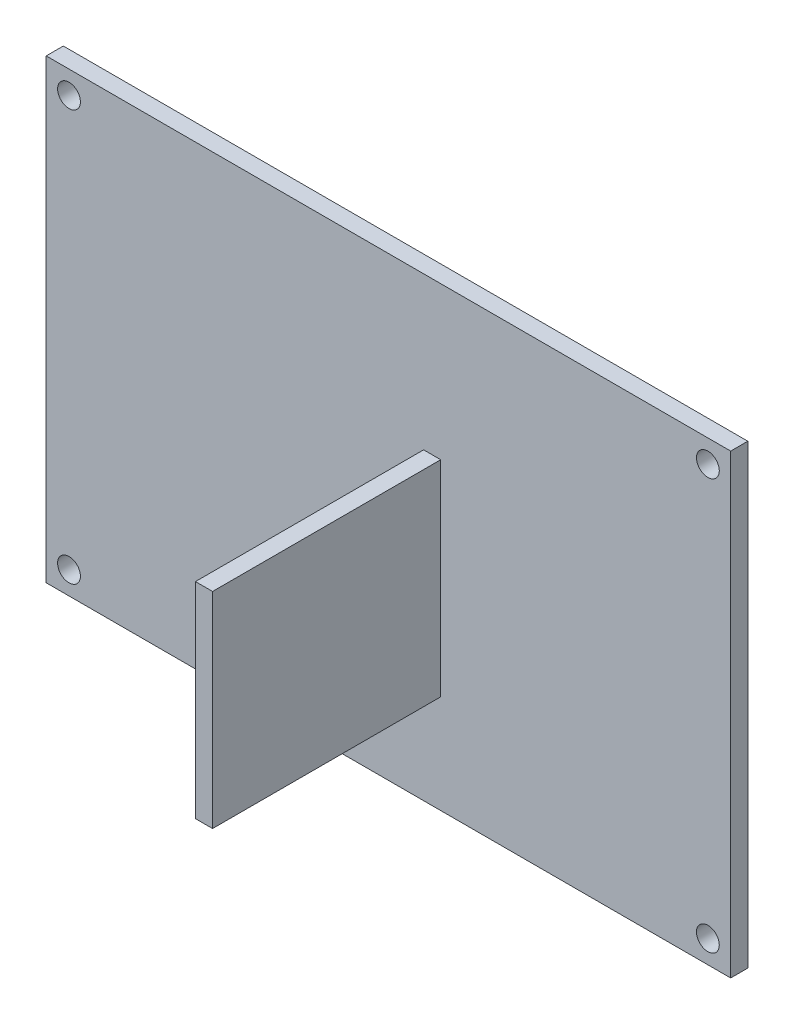
SolidWorks part; units mm, degrees
ref_plane "Plano frontal" through (0, 0, 0) normal (0, 0, 1) x (1, 0, 0)
ref_plane "Plano superior" through (0, 0, 0) normal (0, 1, 0) x (1, 0, 0)
ref_plane "Plano direito" through (0, 0, 0) normal (1, 0, 0) x (0, 0, -1)
sketch "Esboço1" plane through (0, 0, 0) normal (0, 0, 1) x (1, 0, 0)
  line L1 (-30, 20) -> (30, 20)
  line L2 (-30, 20) -> (-30, -20)
  line L3 (-30, -20) -> (30, -20)
  line L4 (30, 20) -> (30, -20)
  line L5 (-30, 20) -> (30, -20) construction
  line L6 (-30, -20) -> (30, 20) construction
  point P0 (0, 0)
  dimension "D1" = 40
  dimension "D2" = 60
extrude "Ressalto-extrusão1" add sketch "Esboço1" along normal blind 1.5
sketch "Esboço2" plane through (0, 0, 1.5) normal (0, 0, 1) x (1, 0, 0)
  line L1 (-28, -18) -> (28, -18) construction
  line L2 (-28, -18) -> (-28, 18) construction
  line L3 (-28, 18) -> (28, 18) construction
  line L4 (28, -18) -> (28, 18) construction
  line L5 (-28, -18) -> (28, 18) construction
  line L6 (-28, 18) -> (28, -18) construction
  circle A0 centre (-28, 18) radius 1
  circle A1 centre (28, 18) radius 1
  circle A2 centre (28, -18) radius 1
  circle A3 centre (-28, -18) radius 1
  point P0 (0, 0)
  dimension "D3" = 2
  dimension "D1" = 56
  dimension "D2" = 36
extrude "Corte-extrusão1" cut sketch "Esboço2" against normal through all
sketch "Esboço3" plane through (0, 0, 1.5) normal (0, 0, 1) x (1, 0, 0)
  line L1 (3.0832, 6.6356) -> (4.5832, 6.6356)
  line L2 (3.0832, 6.6356) -> (3.0832, -11.3644)
  line L3 (3.0832, -11.3644) -> (4.5832, -11.3644)
  line L4 (4.5832, 6.6356) -> (4.5832, -11.3644)
  line L5 (3.0832, 6.6356) -> (4.5832, -11.3644) construction
  line L6 (3.0832, -11.3644) -> (4.5832, 6.6356) construction
  point P0 (3.8332, -2.3644)
  dimension "D1" = 18
  dimension "D2" = 1.5
extrude "Ressalto-extrusão2" add sketch "Esboço3" along normal blind 20
